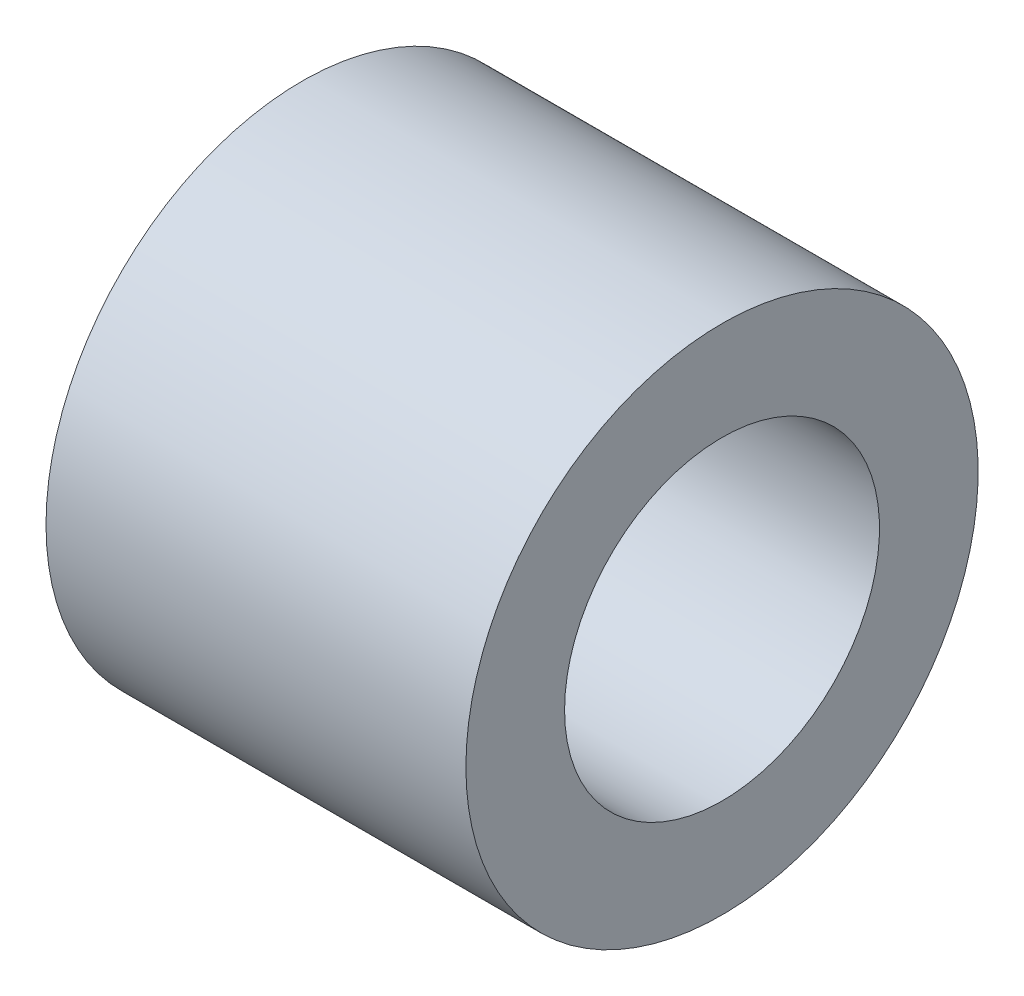
SolidWorks part; units mm, degrees
ref_plane "Front Plane" through (0, 0, 0) normal (0, 0, 1) x (1, 0, 0)
ref_plane "Top Plane" through (0, 0, 0) normal (0, 1, 0) x (1, 0, 0)
ref_plane "Right Plane" through (0, 0, 0) normal (1, 0, 0) x (0, 0, -1)
sketch "Sketch1" plane through (0, 0, 0) normal (0, 1, 0) x (1, 0, 0)
  line L0 (0, 2.3813) -> (6.35, 2.3813)
  line L1 (6.35, 2.3813) -> (6.35, 3.8735)
  line L2 (6.35, 3.8735) -> (0, 3.8735)
  line L3 (0, 3.8735) -> (0, 2.3813)
  line L4 (0, 0) -> (5.3539, 0) construction
  dimension "D1" = 3.8735
  dimension "D2" = 2.3813
  dimension "D3" = 6.35
revolve "Revolve1" add sketch "Sketch1" angle 360 about L4
